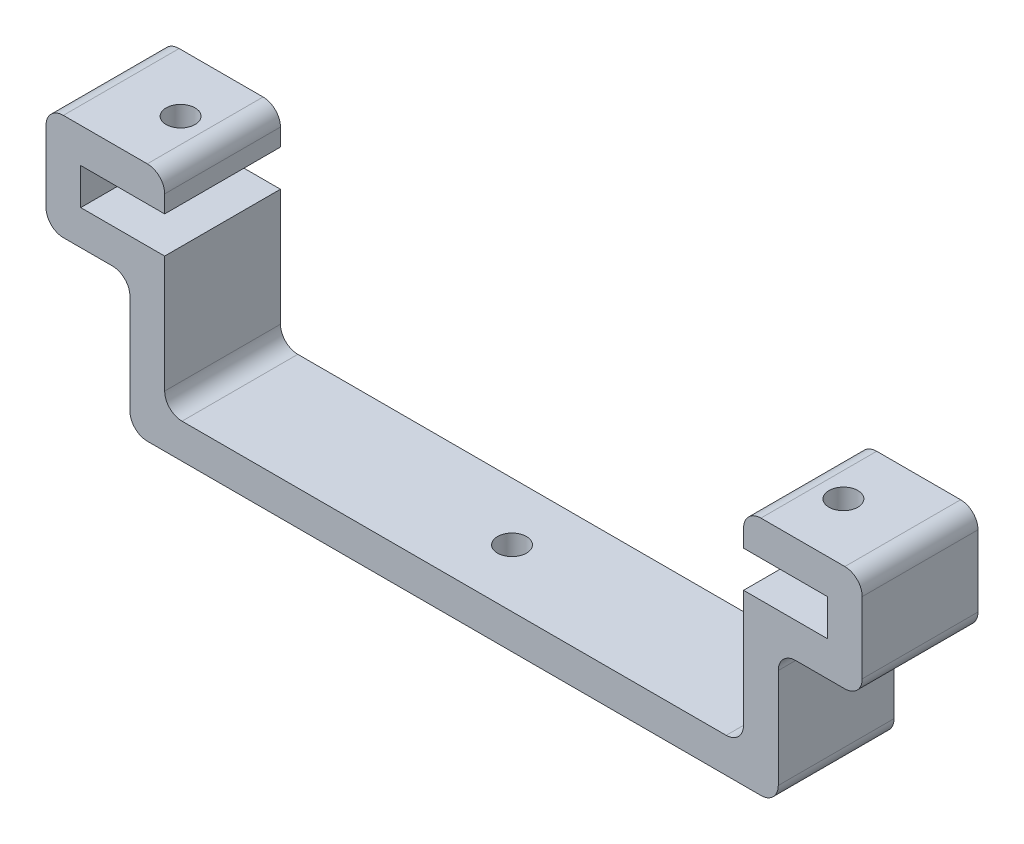
SolidWorks part; units mm, degrees
ref_plane "Front Plane" through (0, 0, 0) normal (0, 0, 1) x (1, 0, 0)
ref_plane "Top Plane" through (0, 0, 0) normal (0, 1, 0) x (1, 0, 0)
ref_plane "Right Plane" through (0, 0, 0) normal (1, 0, 0) x (0, 0, -1)
sketch "Sketch1" plane through (0, 0, 0) normal (0, 0, 1) x (1, 0, 0)
  line L0 (-32.25, 0) -> (-32.25, -3.15)
  line L1 (-32.25, -3.15) -> (-25, -3.15)
  line L3 (-25, -3.15) -> (-25, -14.75)
  line L4 (-25, -14.75) -> (25, -14.75)
  line L5 (25, -14.75) -> (25, -3.15)
  line L6 (-35.25, -6.15) -> (-28, -6.15)
  line L7 (25, -3.15) -> (32.25, -3.15)
  line L8 (32.25, -3.15) -> (32.25, 0)
  line L9 (32.25, 0) -> (25, 0)
  line L11 (25, 0) -> (25, 3)
  line L12 (25, 3) -> (35.25, 3)
  line L13 (35.25, 3) -> (35.25, -6.15)
  line L14 (28, -17.75) -> (-28, -17.75)
  line L15 (-35.25, -6.15) -> (-35.25, 3)
  line L16 (-35.25, 3) -> (-25, 3)
  line L17 (-25, 3) -> (-25, 0)
  line L18 (-25, 0) -> (-32.25, 0)
  line L19 (-28, -6.15) -> (-28, -17.75)
  line L20 (28, -17.75) -> (28, -6.15)
  line L21 (28, -6.15) -> (35.25, -6.15)
  point P2 (0, -14.75)
  point P12 (0, -17.75)
  dimension "D1" = 3
  dimension "D2" = 64.5
  dimension "D3" = 50
  dimension "D4" = 20.75
  dimension "D5" = 3
  dimension "D6" = 3
  dimension "D7" = 3.15
  dimension "D8" = 3
  dimension "D10" = 3
extrude "Boss-Extrude1" add sketch "Sketch1" along normal blind 10
sketch "Sketch4" plane through (0, 3, 0) normal (0, 1, 0) x (1, 0, 0)
  line L1 (-25, -10) -> (-25, 0) construction
  line L2 (28.625, -5) -> (-28.625, -5) construction
  line L3 (25, -10) -> (-25, -10) construction
  line L4 (-25, -10) -> (-32.25, -10) construction
  circle A0 centre (-28.625, -5) radius 1.25
  circle A1 centre (28.625, -5) radius 1.25
  point P7 (-25, -5)
  point P11 (0, -5)
  point P13 (0, -10)
  point P18 (-28.625, -10)
  dimension "D1" = 2.5
extrude "Cut-Extrude2" cut sketch "Sketch4" against normal up to next
sketch "Sketch5" plane through (0, -14.75, 0) normal (0, 1, 0) x (1, 0, 0)
  line L0 (25, 0) -> (-25, 0) construction
  line L1 (-25, -10) -> (-25, 0) construction
  circle A0 centre (0, -5) radius 1.25
  point P5 (0, 0)
  point P9 (-25, -5)
  dimension "D1" = 2.5
extrude "Cut-Extrude3" cut sketch "Sketch5" against normal through all
fillet "Fillet1" radius 1.5 12 edges at (35.25, 3, 5) (-25, -14.75, 5) (25, -14.75, 5) (-35.25, 3, 5) (28, -17.75, 5) (28, -6.15, 5) (35.25, -6.15, 5) (25, 3, 5) (-25, 3, 5) (-28, -17.75, 5) (-28, -6.15, 5) (-35.25, -6.15, 5)
